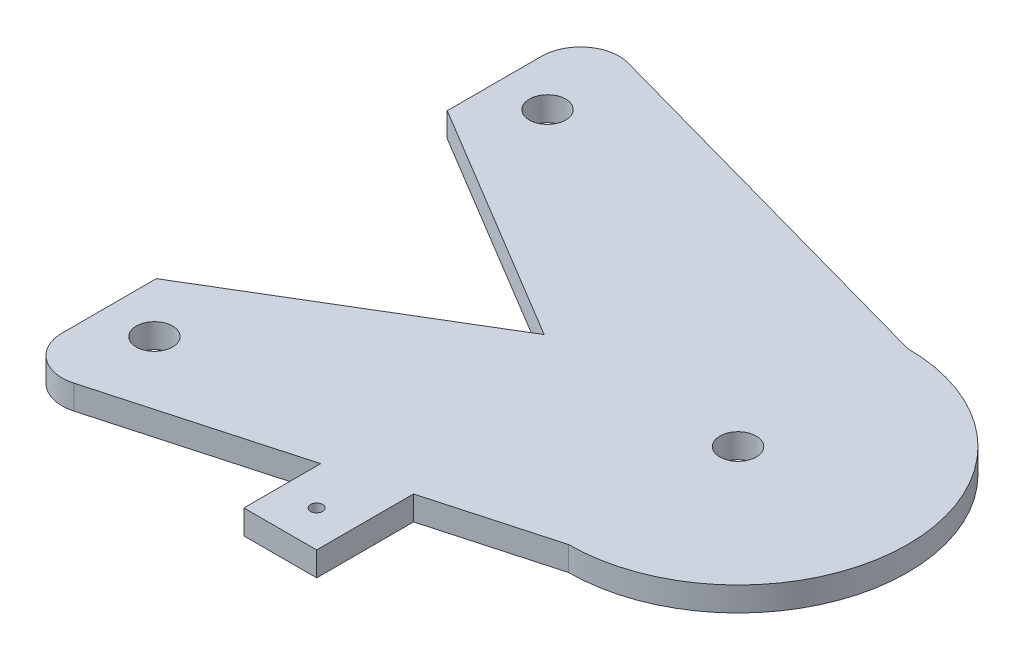
SolidWorks part; units mm, degrees
ref_plane "Front Plane" through (0, 0, 0) normal (0, 0, 1) x (1, 0, 0)
ref_plane "Top Plane" through (0, 0, 0) normal (0, 1, 0) x (1, 0, 0)
ref_plane "Right Plane" through (0, 0, 0) normal (1, 0, 0) x (0, 0, -1)
sketch "Sketch1" plane through (0, 0, 0) normal (0, 1, 0) x (1, 0, 0)
  line L0 (-50.6207, 72.6224) -> (50.8, 44.45)
  line L1 (50.8, 44.45) -> (50.8, -44.45) construction
  line L2 (50.8, -44.45) -> (19.05, -53.2694)
  line L3 (-63.5, 62.8331) -> (-63.5, 38.1)
  line L4 (-63.5, 38.1) -> (0, 0)
  line L6 (0, 0) -> (-63.5, -38.1)
  line L7 (-63.5, -38.1) -> (-63.5, -62.8331)
  line L8 (-50.6207, -72.6224) -> (0, -58.5611)
  line L9 (0, -58.5611) -> (0, -78.6694)
  line L10 (0, -78.6694) -> (19.05, -78.6694)
  line L11 (19.05, -78.6694) -> (19.05, -53.2694)
  line L12 (-63.5, 0) -> (50.8, 0) construction
  line L13 (-63.5, -38.1) -> (-63.5, 38.1) construction
  line L14 (-50.6207, -51.4974) -> (-50.6207, 51.4974) construction
  line L15 (-50.6207, 72.6224) -> (-50.6207, 30.3724) construction
  circle A0 centre (-50.6207, 51.4974) radius 25.4 construction
  circle A1 centre (-50.6207, -51.4974) radius 25.4 construction
  arc A2 (-50.6207, 72.6224) -> (-63.5, 62.8331) centre (-53.34, 62.8331) ccw
  arc A3 (-63.5, -62.8331) -> (-50.6207, -72.6224) centre (-53.34, -62.8331) ccw
  arc A4 (50.8, 44.45) -> (50.8, -44.45) centre (50.8, 0) cw
  circle A5 centre (50.8, 0) radius 4.7625
  circle A6 centre (-50.6207, 51.4974) radius 4.7625
  circle A7 centre (-50.6207, -51.4974) radius 4.7625
  circle A8 centre (9.525, -69.1444) radius 1.5875
  point P19 (-50.6207, 0)
  point P23 (-50.6207, 51.4974)
  point P28 (-63.5, 76.2)
  dimension "D1" = 50.8
  dimension "D6" = 10.16
  dimension "D8" = 10.16
  dimension "D11" = 9.525
  dimension "D12" = 3.175
  dimension "D2" = 88.9
  dimension "D3" = 76.2
  dimension "D4" = 114.3
  dimension "D5" = 38.1
  dimension "D7" = 50.8
  dimension "D9" = 19.05
  dimension "D10" = 25.4
  dimension "D13" = 9.525
  dimension "D14" = 9.525
extrude "Boss-Extrude1" add sketch "Sketch1" along normal blind 6.35
